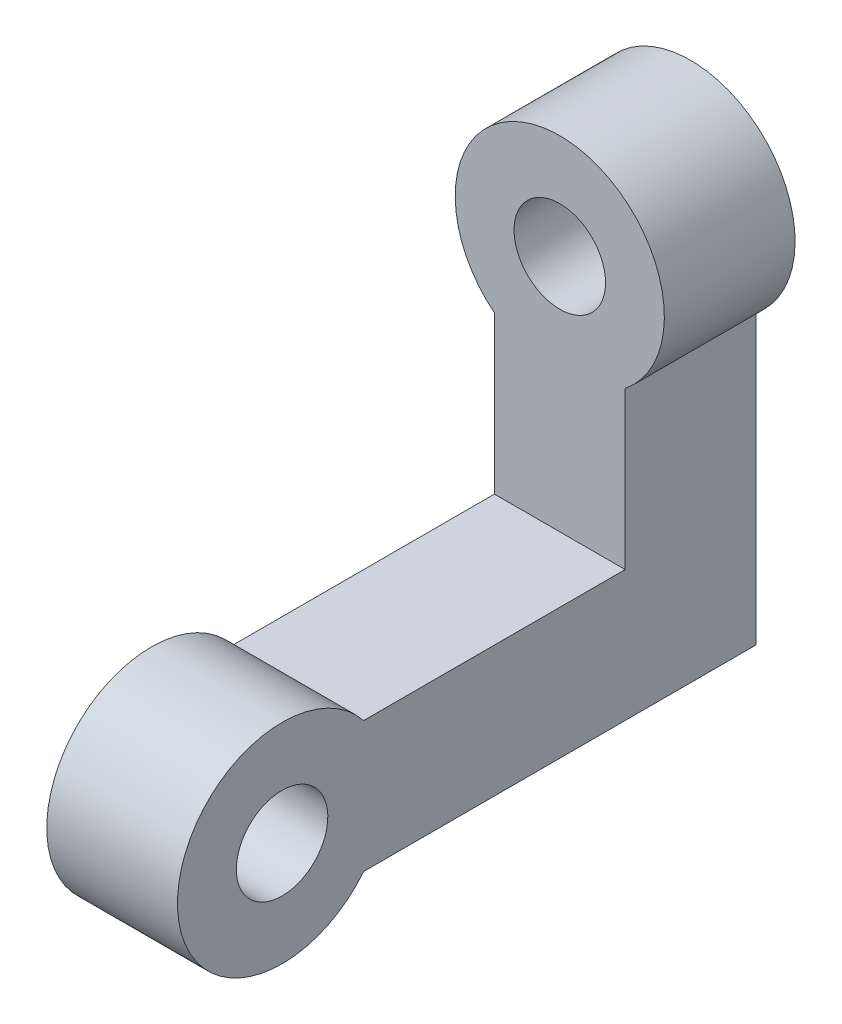
SolidWorks part; units mm, degrees
ref_plane "Plano frontal" through (0, 0, 0) normal (0, 0, 1) x (1, 0, 0)
ref_plane "Plano superior" through (0, 0, 0) normal (0, 1, 0) x (1, 0, 0)
ref_plane "Plano direito" through (0, 0, 0) normal (1, 0, 0) x (0, 0, -1)
sketch "Esboço1" plane through (0, 0, 0) normal (0, 0, 1) x (1, 0, 0)
  line L0 (0, -1.75) -> (0, -7.4521) construction
  line L1 (-2.5, -3.1225) -> (-2.5, -9.1225)
  line L2 (2.5, -3.1225) -> (2.5, -9.1225)
  line L3 (-2.5, -9.1225) -> (2.5, -9.1225)
  arc A0 (2.5, -3.1225) -> (-2.5, -3.1225) centre (0, 0) ccw
  circle A1 centre (0, 0) radius 1.75
  dimension "D1" = 3.5
  dimension "D2" = 8
  dimension "D3" = 5
  dimension "D4" = 6
extrude "Ressalto-extrusão1" add sketch "Esboço1" along normal blind 5
sketch "Esboço2" plane through (-2.5, 0, 0) normal (-1, 0, 0) x (0, 0, 1)
  line L0 (0, -9.1225) -> (0, -14.1225)
  line L1 (0, -14.1225) -> (15, -14.1225)
  line L3 (15, -9.1225) -> (0, -9.1225)
  arc A0 (15, -14.1225) -> (15, -9.1225) centre (18.1225, -11.6225) ccw
  circle A1 centre (18.1225, -11.6225) radius 1.75
  point P6 (0, 0)
  point P7 (0, 0)
  point P10 (0, 0)
  point P11 (14.7948, -9.0837)
  point P12 (0, 0)
  dimension "D1" = 3.5
  dimension "D2" = 8
  dimension "D3" = 5
  dimension "D4" = 15
extrude "Ressalto-extrusão2" add sketch "Esboço2" against normal blind 5
